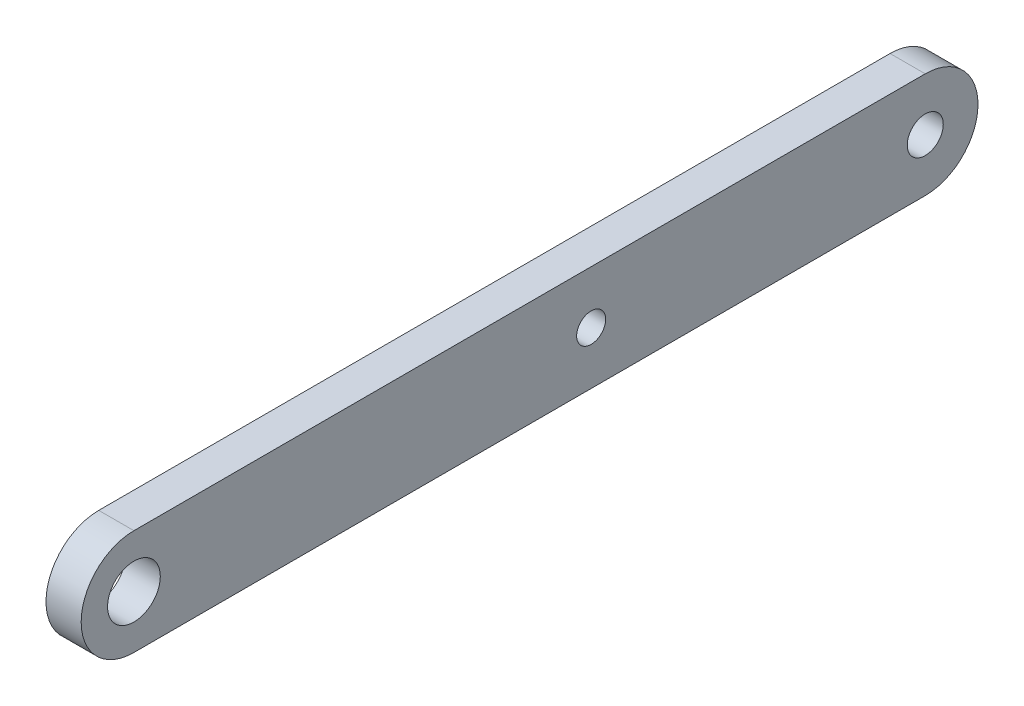
SolidWorks part; units mm, degrees
material "A-玻璃纤维"
ref_plane "前视基准面" through (0, 0, 0) normal (0, 0, 1) x (1, 0, 0)
ref_plane "上视基准面" through (0, 0, 0) normal (0, 1, 0) x (1, 0, 0)
ref_plane "右视基准面" through (0, 0, 0) normal (1, 0, 0) x (0, 0, -1)
sketch "草图1" plane through (0, 0, 0) normal (1, 0, 0) x (0, 0, -1)
  line L0 (0, 0) -> (90, 0) construction
  line L1 (0, 6) -> (90, 6)
  line L2 (0, -6) -> (90, -6)
  circle A0 centre (0, 0) radius 3
  arc A1 (0, 6) -> (0, -6) centre (0, 0) ccw
  arc A2 (90, -6) -> (90, 6) centre (90, 0) ccw
  circle A3 centre (90, 0) radius 2.05
  point P3 (45, 0)
  dimension "D1" = 6
  dimension "D2" = 6
  dimension "D4" = 4.1
  dimension "D3" = 90
extrude "凸台-拉伸1" add sketch "草图1" along normal blind 4
sketch "草图2" plane through (4, 0, 0) normal (1, 0, 0) x (0, 0, -1)
  line L0 (0, 0) -> (90, 0) construction
  circle A0 centre (52, 0) radius 1.65
  dimension "D1" = 3.3
  dimension "D2" = 38
extrude "切除-拉伸1" cut sketch "草图2" against normal through all
